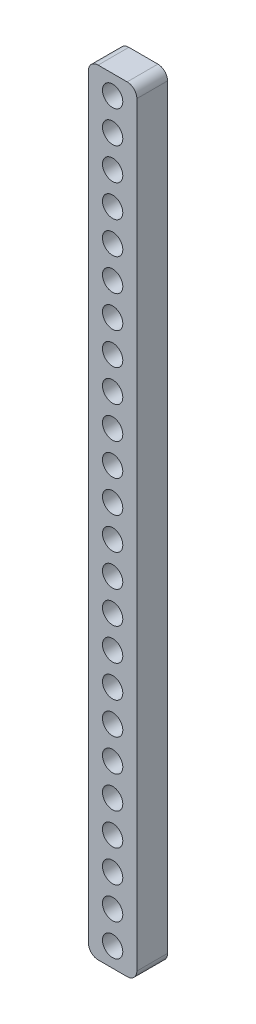
SolidWorks part; units mm, degrees
ref_plane "Front Plane" through (0, 0, 0) normal (0, 0, 1) x (1, 0, 0)
ref_plane "Top Plane" through (0, 0, 0) normal (0, 1, 0) x (1, 0, 0)
ref_plane "Right Plane" through (0, 0, 0) normal (1, 0, 0) x (0, 0, -1)
sketch "Sketch1" plane through (0, 0, 0) normal (0, 0, 1) x (1, 0, 0)
  line L0 (0, -80) -> (0, 80) construction
  line L1 (3, -80) -> (-3, -80)
  line L2 (5, -78) -> (5, 78)
  line L3 (3, 80) -> (-3, 80)
  line L4 (-5, -78) -> (-5, 78)
  line L5 (5, -80) -> (-5, 80) construction
  line L6 (5, 80) -> (-5, -80) construction
  circle A1 centre (0, 76) radius 2.1
  circle A2 centre (0, 69.3913) radius 2.1
  circle A3 centre (0, 62.7826) radius 2.1
  circle A4 centre (0, 56.1739) radius 2.1
  circle A5 centre (0, 49.5652) radius 2.1
  circle A6 centre (0, 42.9565) radius 2.1
  circle A7 centre (0, 36.3478) radius 2.1
  circle A8 centre (0, 29.7391) radius 2.1
  circle A9 centre (0, 23.1304) radius 2.1
  circle A10 centre (0, 16.5217) radius 2.1
  circle A11 centre (0, 9.913) radius 2.1
  circle A12 centre (0, 3.3043) radius 2.1
  circle A13 centre (0, -3.3043) radius 2.1
  circle A14 centre (0, -9.913) radius 2.1
  circle A15 centre (0, -16.5217) radius 2.1
  circle A16 centre (0, -23.1304) radius 2.1
  circle A17 centre (0, -29.7391) radius 2.1
  circle A18 centre (0, -36.3478) radius 2.1
  circle A19 centre (0, -42.9565) radius 2.1
  circle A20 centre (0, -49.5652) radius 2.1
  circle A21 centre (0, -56.1739) radius 2.1
  circle A22 centre (0, -62.7826) radius 2.1
  circle A23 centre (0, -69.3913) radius 2.1
  circle A24 centre (0, -76) radius 2.1
  arc A25 (-3, -80) -> (-5, -78) centre (-3, -78) cw
  arc A26 (3, -80) -> (5, -78) centre (3, -78) ccw
  arc A27 (5, 78) -> (3, 80) centre (3, 78) ccw
  arc A28 (-3, 80) -> (-5, 78) centre (-3, 78) ccw
  point P0 (0, 0)
  dimension "D3" = 4.2
  dimension "D7" = 2
  dimension "D1" = 160
  dimension "D2" = 10
  dimension "D4" = 4
  dimension "D6" = 4
  dimension "D5" = 24
extrude "Boss-Extrude1" add sketch "Sketch1" along normal blind 6.35
